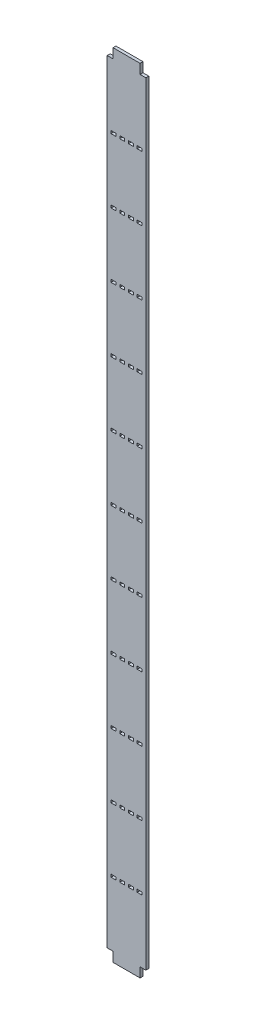
SolidWorks part; units mm, degrees
ref_plane "前视基准面" through (0, 0, 0) normal (0, 0, 1) x (1, 0, 0)
ref_plane "上视基准面" through (0, 0, 0) normal (0, 1, 0) x (1, 0, 0)
ref_plane "右视基准面" through (0, 0, 0) normal (1, 0, 0) x (0, 0, -1)
sketch "草图1" plane through (0, 0, 0) normal (0, 0, 1) x (1, 0, 0)
  line L1 (-10, -205) -> (10, -205)
  line L2 (-10, -205) -> (-10, 205)
  line L3 (-10, 205) -> (10, 205)
  line L4 (10, -205) -> (10, 205)
  line L5 (-10, -205) -> (10, 205) construction
  line L6 (-10, 205) -> (10, -205) construction
  point P0 (0, 0)
  dimension "D1" = 410
  dimension "D2" = 20
extrude "凸台-拉伸1" add sketch "草图1" along normal blind 1.5
sketch "草图2" plane through (0, 0, 1.5) normal (0, 0, 1) x (1, 0, 0)
  line L1 (-10, 205) -> (-7, 205)
  line L2 (-10, 205) -> (-10, 200)
  line L3 (-10, 200) -> (-7, 200)
  line L4 (-7, 205) -> (-7, 200)
  line L5 (-10, 205) -> (-7, 200) construction
  line L6 (-10, 200) -> (-7, 205) construction
  line L7 (10, 205) -> (7, 205)
  line L8 (10, 205) -> (10, 200)
  line L9 (10, 200) -> (7, 200)
  line L10 (7, 205) -> (7, 200)
  line L11 (10, 205) -> (7, 200) construction
  line L12 (10, 200) -> (7, 205) construction
  line L13 (-10, -205) -> (-7, -205)
  line L14 (-10, -205) -> (-10, -200)
  line L15 (-10, -200) -> (-7, -200)
  line L16 (-7, -205) -> (-7, -200)
  line L17 (-10, -205) -> (-7, -200) construction
  line L18 (-10, -200) -> (-7, -205) construction
  line L19 (10, -205) -> (7, -205)
  line L20 (10, -205) -> (10, -200)
  line L21 (10, -200) -> (7, -200)
  line L22 (7, -205) -> (7, -200)
  line L23 (10, -205) -> (7, -200) construction
  line L24 (10, -200) -> (7, -205) construction
  point P4 (-8.5, 202.5)
  point P10 (8.5, 202.5)
  point P16 (-8.5, -202.5)
  point P22 (8.5, -202.5)
  dimension "D1" = 5
  dimension "D2" = 5
  dimension "D3" = 3
  dimension "D4" = 3
  dimension "D5" = 5
  dimension "D6" = 5
  dimension "D7" = 3
  dimension "D8" = 3
extrude "切除-拉伸1" cut sketch "草图2" against normal up to next
sketch "草图3" plane through (0, 0, 1.5) normal (0, 0, 1) x (1, 0, 0)
  line L0 (10, -200) -> (10, 200) construction
  line L1 (-8, -0.7) -> (-5.5, -0.7)
  line L2 (-8, -0.7) -> (-8, 0.7)
  line L3 (-8, 0.7) -> (-5.5, 0.7)
  line L4 (-5.5, -0.7) -> (-5.5, 0.7)
  line L5 (-8, -0.7) -> (-5.5, 0.7) construction
  line L6 (-8, 0.7) -> (-5.5, -0.7) construction
  line L7 (-3.5, -0.7) -> (-1, -0.7)
  line L8 (-3.5, -0.7) -> (-3.5, 0.7)
  line L9 (-3.5, 0.7) -> (-1, 0.7)
  line L10 (-1, -0.7) -> (-1, 0.7)
  line L11 (-3.5, -0.7) -> (-1, 0.7) construction
  line L12 (-3.5, 0.7) -> (-1, -0.7) construction
  line L13 (1, -0.7) -> (3.5, -0.7)
  line L14 (1, -0.7) -> (1, 0.7)
  line L15 (1, 0.7) -> (3.5, 0.7)
  line L16 (3.5, -0.7) -> (3.5, 0.7)
  line L17 (1, -0.7) -> (3.5, 0.7) construction
  line L18 (1, 0.7) -> (3.5, -0.7) construction
  line L19 (5.5, -0.7) -> (8, -0.7)
  line L20 (5.5, -0.7) -> (5.5, 0.7)
  line L21 (5.5, 0.7) -> (8, 0.7)
  line L22 (8, -0.7) -> (8, 0.7)
  line L23 (5.5, -0.7) -> (8, 0.7) construction
  line L24 (5.5, 0.7) -> (8, -0.7) construction
  line L25 (-10, 200) -> (-10, -200) construction
  point P0 (-6.75, 0)
  point P5 (-2.25, 0)
  point P10 (2.25, 0)
  point P15 (6.75, 0)
  dimension "D1" = 2
  dimension "D2" = 2.5
  dimension "D3" = 2.5
  dimension "D4" = 2.5
  dimension "D5" = 2.5
  dimension "D6" = 2
  dimension "D7" = 2
  dimension "D8" = 2
  dimension "D9" = 1.4
  dimension "D10" = 1.4
  dimension "D11" = 1.4
  dimension "D12" = 1.4
extrude "切除-拉伸2" cut sketch "草图3" against normal up to next (1.5 mm away)
pattern_linear "阵列(线性)1" count 6 spacing 33.33 along (0, -1, 0) count 6 spacing 33.33 along (0, 1, 0) of "切除-拉伸2"
